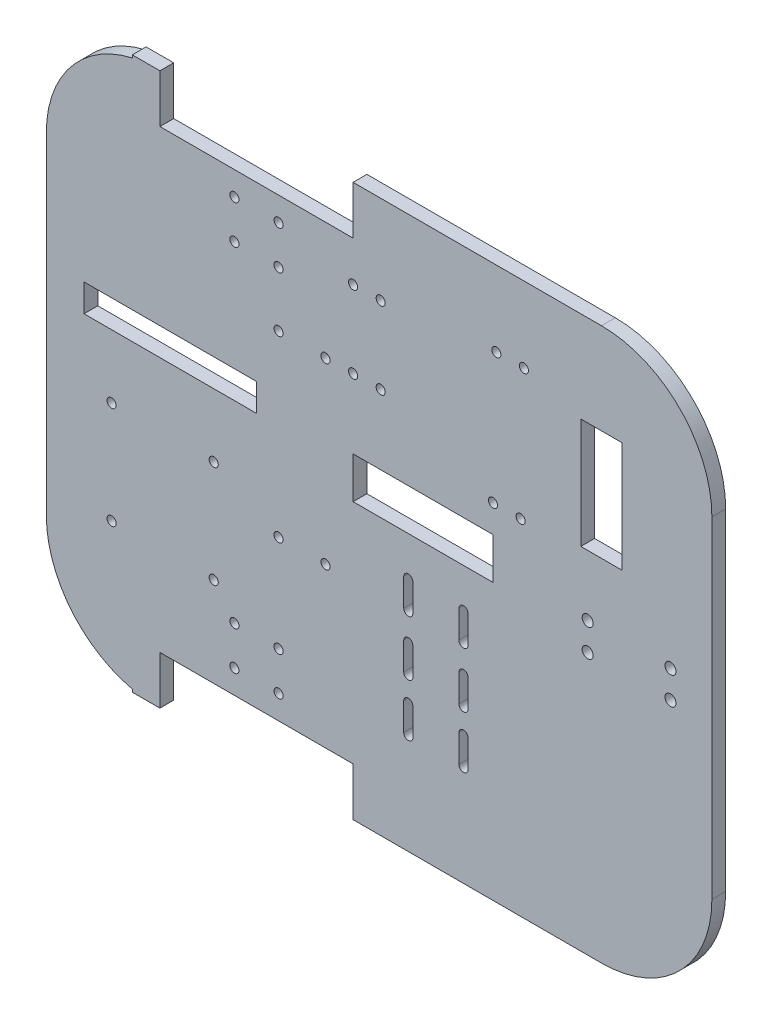
SolidWorks part; units mm, degrees
ref_plane "Front Plane" through (0, 0, 0) normal (0, 0, 1) x (1, 0, 0)
ref_plane "Top Plane" through (0, 0, 0) normal (0, 1, 0) x (1, 0, 0)
ref_plane "Right Plane" through (0, 0, 0) normal (1, 0, 0) x (0, 0, -1)
sketch "Sketch1" plane through (0, 0, 0) normal (0, 0, 1) x (1, 0, 0)
  line L0 (0, 0) -> (-30, 0)
  line L1 (-95, 100) -> (95, 100)
  line L2 (-135, 60) -> (-135, -60)
  line L3 (-95, -100) -> (95, -100)
  line L4 (135, 60) -> (135, -60)
  line L5 (-135, 100) -> (135, -100) construction
  line L6 (-135, -100) -> (135, 100) construction
  line L7 (-30, -100) -> (-30, 100)
  line L8 (-60, -82.5) -> (0, -117.5) construction
  line L9 (-60, 117.5) -> (0, 117.5)
  line L10 (-60, 117.5) -> (-60, 82.5)
  line L11 (-60, 82.5) -> (0, 82.5)
  line L12 (0, 117.5) -> (0, 82.5)
  line L13 (-60, 117.5) -> (0, 82.5) construction
  line L14 (-60, 82.5) -> (0, 117.5) construction
  line L15 (-60, -117.5) -> (0, -82.5) construction
  line L16 (0, -117.5) -> (0, -82.5)
  line L17 (-60, -82.5) -> (0, -82.5)
  line L18 (-60, -117.5) -> (-60, -82.5)
  line L19 (-60, -117.5) -> (0, -117.5)
  arc A0 (-95, -100) -> (-135, -60) centre (-95, -60) cw
  arc A1 (135, -60) -> (95, -100) centre (95, -60) cw
  arc A2 (135, 60) -> (95, 100) centre (95, 60) ccw
  arc A3 (-95, 100) -> (-135, 60) centre (-95, 60) ccw
  point P0 (0, 0)
  dimension "D3" = 40
  dimension "D1" = 270
  dimension "D2" = 200
  dimension "D4" = 30
  dimension "D5" = 60
  dimension "D6" = 35
extrude "Boss-Extrude1" add sketch "Sketch1" along normal blind 10
sketch "Sketch2" plane through (0, 0, 0) normal (0, 0, -1) x (-1, 0, 0)
  line L0 (-95, 87.5) -> (95, 87.5)
  line L1 (-95, 100) -> (0, 100)
  line L2 (-95, 100) -> (-95, 82.5)
  line L3 (-95, 82.5) -> (0, 82.5)
  line L4 (0, 100) -> (0, 82.5)
  line L5 (60, 82.5) -> (95, 82.5)
  line L6 (60, 82.5) -> (60, 100)
  line L7 (60, 100) -> (95, 100)
  line L8 (95, 82.5) -> (95, 100)
  line L9 (-135, 0) -> (135, 0)
  line L10 (-135, 60) -> (-135, -60) construction
  line L11 (135, 60) -> (135, -60) construction
  line L12 (60, -82.5) -> (95, -82.5)
  line L13 (95, -82.5) -> (95, -100)
  line L14 (-95, -100) -> (-95, -82.5)
  line L15 (-95, -82.5) -> (0, -82.5)
  line L16 (-95, -87.5) -> (95, -87.5)
  circle A0 centre (-60, 87.5) radius 1.475
  circle A1 centre (-25, 87.5) radius 1.475
  circle A2 centre (77.5, 87.5) radius 1.475
  circle A3 centre (77.5, -87.5) radius 1.475
  circle A4 centre (-25, -87.5) radius 1.475
  circle A5 centre (-60, -87.5) radius 1.475
  point P20 (-60, 87.5)
  point P21 (-25, 87.5)
  point P22 (77.5, 87.5)
  dimension "D5" = 2.95
  dimension "D1" = 5
  dimension "D2" = 35
  dimension "D3" = 17.5
  dimension "D4" = 35
extrude "Cut-Extrude1" cut sketch "Sketch2" against normal blind 10 contours L0 A0 | L0 A0 | L0 A1 | L0 A1 | L0 A2 | L0 A2 | A3 L16 | A3 L16 | A5 L16 | A5 L16 | A4 L16 | A4 L16
sketch3d "3DSketch1"
  line L3 (135, 60, 0) -> (-135, 60, 0)
  line L4 (135, 60, 0) -> (135, 60, 5)
  line L5 (135, 60, 10) -> (135, 60, 0) construction
  line L6 (135, 60, 5) -> (-135, 60, 5)
  line L7 (-135, 60, 0) -> (-135, 60, 5)
extrude "Cut-Extrude2" cut sketch "3DSketch1" along direction (0, 1, 0) on the side against the normal through all and the other way through all
sketch "Sketch5" plane through (0, 0, 5) normal (0, 0, -1) x (-1, 0, 0)
  line L0 (95, -100) -> (60, -100) construction
  line L1 (60, -82.5) -> (65, -82.5)
  line L2 (60, -82.5) -> (60, -100)
  line L3 (60, -100) -> (65, -100)
  line L4 (65, -82.5) -> (65, -100)
  line L5 (0, -100) -> (-95, -100) construction
  line L6 (0, -82.5) -> (-5, -82.5)
  line L7 (0, -82.5) -> (0, -100)
  line L8 (0, -100) -> (-5, -100)
  line L9 (-5, -82.5) -> (-5, -100)
  line L10 (135, 0) -> (-135, 0) construction
  line L11 (135, -60) -> (135, 60) construction
  line L12 (-135, -60) -> (-135, 60) construction
  line L13 (-5, 82.5) -> (-5, 100)
  line L14 (0, 100) -> (-5, 100)
  line L15 (0, 82.5) -> (0, 100)
  line L16 (0, 82.5) -> (-5, 82.5)
  line L17 (65, 82.5) -> (65, 100)
  line L18 (60, 100) -> (65, 100)
  line L19 (60, 82.5) -> (60, 100)
  line L20 (60, 82.5) -> (65, 82.5)
  line L21 (-95, 19.5) -> (-95, -19.5)
  circle A0 centre (-95, -19.5) radius 1.5
  circle A1 centre (-95, 19.5) radius 1.5
  point P28 (-95, 0)
  point P32 (-95, 0)
  dimension "D5" = 3
  dimension "D1" = 5
  dimension "D2" = 5
  dimension "D3" = 40
  dimension "D4" = 39
sketch "Sketch6" plane through (0, 0, 5) normal (0, 0, -1) x (-1, 0, 0)
  line L0 (60, -82.5) -> (0, -82.5)
  line L1 (30, -82.5) -> (30, -52.8)
  line L2 (38, -73.87) -> (22, -73.87)
  line L3 (38, -73.87) -> (38, -59.87)
  line L4 (22, -73.87) -> (22, -59.87)
  line L5 (-95, 28.5) -> (-95, -28.5)
  line L6 (135, 0) -> (-135, 0) construction
  line L7 (22, 73.87) -> (22, 59.87)
  line L8 (38, 73.87) -> (38, 59.87)
  line L9 (38, 73.87) -> (22, 73.87)
  line L10 (30, 82.5) -> (30, 52.8)
  line L11 (60, 82.5) -> (0, 82.5)
  line L13 (65, -100) -> (60, -100)
  line L14 (65, -100) -> (65, -82.5)
  line L15 (65, -82.5) -> (60, -82.5)
  line L16 (60, -100) -> (60, -82.5)
  line L17 (0, -100) -> (-5, -100)
  line L18 (0, -100) -> (0, -82.5)
  line L19 (0, -82.5) -> (-5, -82.5)
  line L20 (-5, -100) -> (-5, -82.5)
  line L21 (65, 82.5) -> (60, 82.5)
  line L22 (65, 82.5) -> (65, 100)
  line L23 (65, 100) -> (60, 100)
  line L24 (60, 82.5) -> (60, 100)
  line L25 (0, 82.5) -> (-5, 82.5)
  line L26 (0, 82.5) -> (0, 100)
  line L27 (0, 100) -> (-5, 100)
  line L28 (-5, 82.5) -> (-5, 100)
  circle A0 centre (38, -73.87) radius 1.65
  circle A1 centre (38, -59.87) radius 1.65
  circle A2 centre (22, -59.87) radius 1.65
  circle A3 centre (22, -73.87) radius 1.65
  circle A4 centre (22, 73.87) radius 1.65
  circle A5 centre (22, 59.87) radius 1.65
  circle A6 centre (38, 59.87) radius 1.65
  circle A7 centre (38, 73.87) radius 1.65
  circle A8 centre (-95, -28.5) radius 1.5
  circle A9 centre (-95, 28.5) radius 1.5
  point P6 (30, -73.87)
  point P10 (30, -73.87)
  point P32 (30, 73.87)
  point P33 (-95, 0)
  point P38 (-95, 0)
  dimension "D5" = 3.3
  dimension "D7" = 3
  dimension "D1" = 29.7
  dimension "D2" = 8.63
  dimension "D3" = 16
  dimension "D4" = 14
  dimension "D6" = 57
extrude "motor" cut sketch "Sketch6" against normal through all
sketch "Sketch7" plane through (0, 0, 10) normal (0, 0, 1) x (1, 0, 0)
  line L0 (95, -28.5) -> (95, 28.5)
  line L1 (95, -40) -> (95, 40)
  line L2 (-65, 0) -> (-95, 0)
  line L3 (-92.5, -50) -> (-82.5, -50) construction
  line L4 (5, 82.5) -> (-65, 82.5)
  line L5 (5, 82.5) -> (5, -82.5)
  line L6 (5, -82.5) -> (-65, -82.5)
  line L7 (-65, 82.5) -> (-65, -82.5)
  line L9 (-30, 82.5) -> (-30, -82.5)
  line L10 (5, 0) -> (135, 0)
  line L11 (135, 60) -> (135, -60) construction
  line L12 (72.5, 50) -> (67.5, 50)
  line L13 (72.5, 50) -> (72.5, -50)
  line L14 (72.5, -50) -> (67.5, -50)
  line L15 (67.5, 50) -> (67.5, -50)
  line L16 (72.5, 50) -> (67.5, -50) construction
  line L17 (72.5, -50) -> (67.5, 50) construction
  line L18 (-82.5, -50) -> (-45.5, -50)
  line L19 (-92.5, 50) -> (-97.5, 50)
  line L20 (-92.5, 50) -> (-92.5, -50)
  line L21 (-92.5, -50) -> (-97.5, -50)
  line L22 (-97.5, 50) -> (-97.5, -50)
  line L23 (-92.5, 50) -> (-97.5, -50) construction
  line L24 (-92.5, -50) -> (-97.5, 50) construction
  line L25 (-82.5, -50) -> (-82.5, -13)
  line L26 (-82.5, -13) -> (-45.5, -13)
  line L27 (-45.5, -50) -> (-45.5, -13)
  line L31 (5, 67.9) -> (56.9, 72.6507)
  line L32 (56.9, 72.6507) -> (55.7, 24.7893)
  line L33 (55.7, 24.7893) -> (5, 40)
  line L35 (-92.5, 20) -> (-22.5, 20)
  line L36 (-92.5, 20) -> (-92.5, 10)
  line L37 (-92.5, 10) -> (-22.5, 10)
  line L38 (-22.5, 20) -> (-22.5, 10)
  circle A0 centre (95, -40) radius 1.5
  circle A1 centre (95, 40) radius 1.5
  circle A2 centre (-45.5, -13) radius 1.65
  circle A3 centre (-82.5, -13) radius 1.65
  circle A4 centre (-45.5, -50) radius 1.65
  circle A5 centre (-82.5, -50) radius 1.65
  circle A6 centre (56.9, 72.6507) radius 1.65
  circle A7 centre (55.7, 24.7893) radius 1.65
  circle A8 centre (5, 40) radius 1.65
  circle A9 centre (5, 67.9) radius 1.65
  circle A10 centre (-22, 59.87) radius 1.5
  circle A11 centre (-22, 73.87) radius 1.5
  circle A12 centre (-22, -59.87) radius 1.5
  circle A13 centre (-22, -73.87) radius 1.5
  point P7 (95, 0)
  point P14 (-30, 0)
  point P17 (70, 0)
  point P18 (70, 0)
  point P43 (5, 40)
  point P45 (5, 67.9)
  point P53 (-92.5, 20)
  dimension "D2" = 3
  dimension "D12" = 3.3
  dimension "D19" = 3.3
  dimension "D1" = 80
  dimension "D3" = 100
  dimension "D4" = 5
  dimension "D5" = 100
  dimension "D6" = 5
  dimension "D7" = 100
  dimension "D8" = 30
  dimension "D9" = 10
  dimension "D10" = 37
  dimension "D11" = 37
  dimension "D13" = 40
  dimension "D14" = 95.23
  dimension "D15" = 106.7
  dimension "D16" = 27.9
  dimension "D17" = 51.9
  dimension "D18" = 50.7
  dimension "D20" = 30
  dimension "D21" = 70
  dimension "D22" = 10
extrude "adn1_banhbi_l298" cut sketch "Sketch7" against normal blind 10
sketch "Sketch10" plane through (0, 0, 10) normal (0, 0, 1) x (1, 0, 0)
  line L1 (-106.1528, 60) -> (-106.1528, -60)
  line L10 (-65, 100) -> (-66.1528, 100)
  line L11 (-65, 100) -> (-65, -100)
  line L16 (-65, -100) -> (-66.1528, -100)
  line L17 (-147.3055, 100) -> (-147.3055, -100)
  line L18 (-75, 100) -> (-75, -100)
  line L19 (-65, 100) -> (-147.3055, 100)
  line L20 (-65, 100) -> (-65, -100)
  line L21 (-65, -100) -> (-147.3055, -100)
  line L22 (-147.3055, 100) -> (-147.3055, -100)
  line L24 (-65, 100) -> (-135, 100)
  line L25 (-65, 100) -> (-65, -100)
  line L26 (-65, -100) -> (-135, -100)
  line L27 (-135, 100) -> (-135, -100)
  arc A2 (-66.1528, -100) -> (-106.1528, -60) centre (-66.1528, -60) cw
  arc A3 (-106.1528, 60) -> (-66.1528, 100) centre (-66.1528, 60) cw
  line M30 (-65, 100) -> (-95, 100)
  arc M31 (-95, 100) -> (-135, 60) centre (-95, 60) ccw
  line M32 (-135, 60) -> (-135, -60)
  arc M33 (-135, -60) -> (-95, -100) centre (-95, -60) ccw
  line M34 (-95, -100) -> (-65, -100)
  dimension "D1" = 40
  dimension "D2" = 10
extrude "Cut-Extrude8" cut sketch "Sketch10" against normal blind 10 contours L1 A3 L18 A2 M30 M31 M32 M33 M34
sketch "batterry_angten" plane through (0, 0, 10) normal (0, 0, 1) x (1, 0, 0)
  line L0 (-22, 73.87) -> (-22, 59.87)
  line L1 (-22, 59.87) -> (-22, 39.87)
  line L2 (-22, -73.87) -> (-22, -59.87)
  line L3 (-22, -59.87) -> (-22, -24.87)
  line L4 (-22, 39.87) -> (-5, 39.87)
  line L5 (-22, -24.87) -> (-5, -24.87)
  line L6 (-30, 20) -> (135, 20)
  line L7 (135, 60) -> (135, -60) construction
  line L8 (-30, 10) -> (135, 10) construction
  line L9 (55.7, 24.7893) -> (55.7, -0.2107)
  line L10 (55.7, 14.7893) -> (5, 14.7893)
  line L11 (5, 14.7893) -> (5, -0.2107)
  line L12 (5, -0.2107) -> (55.7, -0.2107)
  line L13 (25, -87.5) -> (45, -87.5)
  line L14 (45, -87.5) -> (45, -19.5)
  line L16 (55.7, 14.7893) -> (5, 14.7893)
  line L17 (55.7, 14.7893) -> (55.7, -0.2107)
  line L18 (55.7, -0.2107) -> (5, -0.2107)
  line L19 (5, 14.7893) -> (5, -0.2107)
  line L20 (46.65, -14.5) -> (43.35, -14.5)
  line L21 (46.65, -14.5) -> (46.65, -24.5)
  line L22 (46.65, -24.5) -> (43.35, -24.5)
  line L23 (43.35, -14.5) -> (43.35, -24.5)
  line L24 (46.65, -14.5) -> (43.35, -24.5) construction
  line L25 (46.65, -24.5) -> (43.35, -14.5) construction
  line L29 (46.65, -34.5) -> (43.35, -34.5)
  line L30 (46.65, -34.5) -> (46.65, -44.5)
  line L31 (46.65, -53.5) -> (43.35, -53.5)
  line L32 (46.65, -53.5) -> (46.65, -63.5)
  line L33 (46.65, -63.5) -> (43.35, -63.5)
  line L34 (43.35, -53.5) -> (43.35, -63.5)
  line L35 (46.65, -53.5) -> (43.35, -63.5) construction
  line L36 (46.65, -63.5) -> (43.35, -53.5) construction
  line L41 (35, -87.5) -> (35, -4.5) construction
  line L42 (25, -87.5) -> (25, -19.5)
  line L43 (46.65, -44.5) -> (43.35, -44.5)
  line L44 (43.35, -34.5) -> (43.35, -44.5)
  line L45 (46.65, -34.5) -> (43.35, -44.5) construction
  line L46 (46.65, -44.5) -> (43.35, -34.5) construction
  line L47 (23.35, -14.5) -> (23.35, -24.5)
  line L48 (26.65, -14.5) -> (26.65, -24.5)
  line L49 (23.35, -14.5) -> (26.65, -14.5)
  line L50 (23.35, -44.5) -> (26.65, -34.5) construction
  line L51 (23.35, -34.5) -> (26.65, -44.5) construction
  line L52 (23.35, -63.5) -> (26.65, -53.5) construction
  line L53 (23.35, -53.5) -> (26.65, -63.5) construction
  line L54 (26.65, -34.5) -> (26.65, -44.5)
  line L55 (23.35, -44.5) -> (26.65, -44.5)
  line L56 (26.65, -53.5) -> (26.65, -63.5)
  line L57 (23.35, -63.5) -> (26.65, -63.5)
  line L58 (23.35, -53.5) -> (23.35, -63.5)
  line L59 (23.35, -53.5) -> (26.65, -53.5)
  line L60 (23.35, -34.5) -> (23.35, -44.5)
  line L61 (23.35, -34.5) -> (26.65, -34.5)
  line L62 (23.35, -24.5) -> (26.65, -24.5)
  circle A0 centre (-22, 73.87) radius 1.5
  circle A1 centre (-22, 59.87) radius 1.5
  circle A2 centre (-22, -73.87) radius 1.5
  circle A3 centre (-22, -59.87) radius 1.5
  circle A4 centre (-22, 39.87) radius 1.65
  circle A6 centre (-22, -24.87) radius 1.65
  circle A10 centre (-5, 39.87) radius 1.65
  circle A11 centre (-5, -24.87) radius 1.65
  circle A12 centre (55.7, 24.7893) radius 1.5
  circle A13 centre (25, -87.5) radius 1.475
  circle A14 centre (45, -14.5) radius 1.65
  circle A16 centre (45, -24.5) radius 1.65
  circle A19 centre (45, -53.5) radius 1.65
  circle A20 centre (45, -63.5) radius 1.65
  circle A23 centre (45, -34.5) radius 1.65
  circle A24 centre (45, -44.5) radius 1.65
  circle A25 centre (45, -77.5) radius 1.65
  circle A26 centre (25, -77.5) radius 1.65
  circle A27 centre (25, -14.5) radius 1.65
  circle A28 centre (25, -44.5) radius 1.65
  circle A29 centre (25, -34.5) radius 1.65
  circle A30 centre (25, -63.5) radius 1.65
  circle A31 centre (25, -53.5) radius 1.65
  circle A32 centre (25, -24.5) radius 1.65
  point P31 (55.7, 14.7893)
  point P40 (45, -77.5)
  point P43 (45, -58.5)
  point P44 (45, -39.5)
  point P72 (45, -58.5)
  point P82 (45, -39.5)
  point P102 (25, -39.5)
  point P103 (25, -58.5)
  point P104 (25, -77.5)
  dimension "D4" = 3.3
  dimension "D12" = 3.3
  dimension "D16" = 3.3
  dimension "D1" = 20
  dimension "D2" = 17
  dimension "D3" = 10
  dimension "D5" = 35
  dimension "D6" = 15
  dimension "D7" = 20
  dimension "D8" = 10
  dimension "D9" = 19
  dimension "D10" = 19
  dimension "D11" = 20
  dimension "D13" = 10
  dimension "D14" = 0
  dimension "D15" = 0
sketch "Sketch14" plane through (0, 0, 10) normal (0, 0, 1) x (1, 0, 0)
  line L0 (5, 67.9) -> (5, 40) construction
  line L1 (5, 40) -> (55.7, 24.7893) construction
  line L2 (55.7, 24.7893) -> (56.9, 72.6507) construction
  line L3 (56.9, 72.6507) -> (5, 67.9) construction
  line L4 (5, 67.9) -> (15, 67.9)
  line L5 (5, 40) -> (15, 40)
  line L6 (15, 67.9) -> (15, 40)
  line L7 (15, 40) -> (65.7, 24.7893)
  line L8 (65.7, 24.7893) -> (66.9, 72.6507)
  line L9 (66.9, 72.6507) -> (15, 67.9)
  circle A0 centre (66.9, 72.6507) radius 1.65
  circle A1 centre (65.7, 24.7893) radius 1.65
  circle A2 centre (15, 67.9) radius 1.65
  circle A3 centre (15, 40) radius 1.65
  dimension "D5" = 3.3
  dimension "D1" = 10
  dimension "D2" = 0
  dimension "D3" = 51.9
  dimension "D4" = 50.7
extrude "Cut-Extrude9" cut sketch "Sketch14" against normal blind 10 contours L8 A0 L9 | L9 A0 L8 | L7 A1 L8 | L8 A1 L7 | L5 A3 L7 | L7 A3 L6 | L6 A3 L5 | L4 A2 L6 | L6 A2 L9 | L9 A2 L4
sketch "Sketch15" plane through (0, 0, 10) normal (0, 0, 1) x (1, 0, 0)
  line L0 (135, 60) -> (135, -60)
  line L1 (135, 0) -> (-106.1528, 0)
  line L2 (-106.1528, 60) -> (-106.1528, -60) construction
  line L3 (135, 5) -> (90, 5)
  line L4 (135, -5) -> (90, -5)
  circle A2 centre (120, 5) radius 2
  circle A3 centre (90, 5) radius 2
  circle A4 centre (90, -5) radius 2
  circle A5 centre (120, -5) radius 2
  point P8 (135, 5)
  point P11 (120, 5)
  dimension "D3" = 15
  dimension "D4" = 4
  dimension "D1" = 5
  dimension "D2" = 45
extrude "banh_truoc" cut sketch "Sketch15" against normal blind 10
sketch "Sketch16" plane through (0, 0, 5) normal (0, 0, -1) x (-1, 0, 0)
  line L0 (-135, -60) -> (106.1528, -60)
  line L1 (-5, -100) -> (-5, 100)
sketch "Sketch17" plane through (0, 0, 10) normal (0, 0, 1) x (1, 0, 0)
  line L0 (95, 28.5) -> (95, 27)
  line L1 (87.5, 27) -> (102.5, 27)
  line L3 (87.5, 27) -> (102.5, 27)
  line L4 (87.5, 27) -> (87.5, 67)
  line L5 (87.5, 67) -> (102.5, 67)
  line L6 (102.5, 27) -> (102.5, 67)
  circle A0 centre (95, 28.5) radius 1.5 construction
  point P8 (95, 27)
  dimension "D1" = 15
  dimension "D2" = 40
extrude "adn" cut sketch "Sketch17" against normal blind 10
extrude "battery_angten" cut sketch "batterry_angten" along direction (0, 0, 1) on the side against the normal blind 10
sketch "Sketch18" plane through (0, 0, 10) normal (0, 0, 1) x (1, 0, 0)
  circle A0 centre (-77.5, -87.5) radius 1.475
  circle A1 centre (-77.5, 87.5) radius 1.475
  circle A2 centre (95, -28.5) radius 1.5
  circle A3 centre (95, -40) radius 1.5
  circle A4 centre (60, -87.5) radius 1.475
  circle A5 centre (25, -87.5) radius 1.475
  circle A6 centre (60, 87.5) radius 1.475
  circle A7 centre (25, 87.5) radius 1.475
extrude "Boss-Extrude2" add sketch "Sketch18" against normal up to surface (5 mm away) up to face at (45, -19.5, 5)
